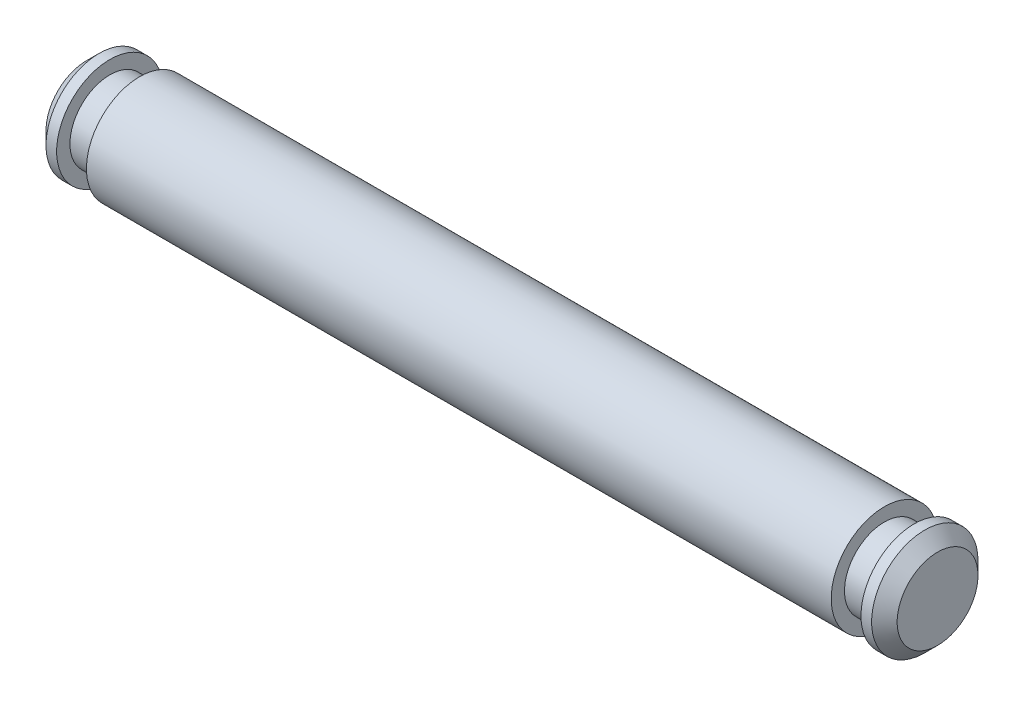
SolidWorks part; units mm, degrees
material "Plain Carbon Steel"
ref_plane "Front Plane" through (0, 0, 0) normal (0, 0, 1) x (1, 0, 0)
ref_plane "Top Plane" through (0, 0, 0) normal (0, 1, 0) x (1, 0, 0)
ref_plane "Right Plane" through (0, 0, 0) normal (1, 0, 0) x (0, 0, -1)
sketch "Sketch1" plane through (0, 0, 0) normal (0, 0, 1) x (1, 0, 0)
  line L0 (0, 0) -> (50.8, 0)
  line L1 (50.8, 0) -> (50.8, 2.413)
  line L2 (50.8, 2.413) -> (50.038, 3.175)
  line L3 (50.038, 3.175) -> (49.403, 3.175)
  line L4 (49.403, 3.175) -> (49.403, 2.3813)
  line L5 (49.403, 2.3813) -> (47.625, 2.3813)
  line L6 (47.625, 2.3813) -> (47.625, 3.175)
  line L7 (47.625, 3.175) -> (3.175, 3.175)
  line L8 (3.175, 3.175) -> (3.175, 2.3813)
  line L9 (3.175, 2.3813) -> (1.397, 2.3813)
  line L10 (1.397, 2.3813) -> (1.397, 3.175)
  line L11 (1.397, 3.175) -> (0.762, 3.175)
  line L12 (0.762, 3.175) -> (0, 2.413)
  line L13 (0, 2.413) -> (0, 0)
  line L14 (0, 0) -> (-4.8683, 0) construction
  dimension "D1" = 6.35
  dimension "D2" = 50.8
  dimension "D3" = 0.762
  dimension "D4" = 1.778
  dimension "D5" = 44.45
  dimension "D6" = 4.7625
revolve "Revolve1" add sketch "Sketch1" angle 360 about L14
